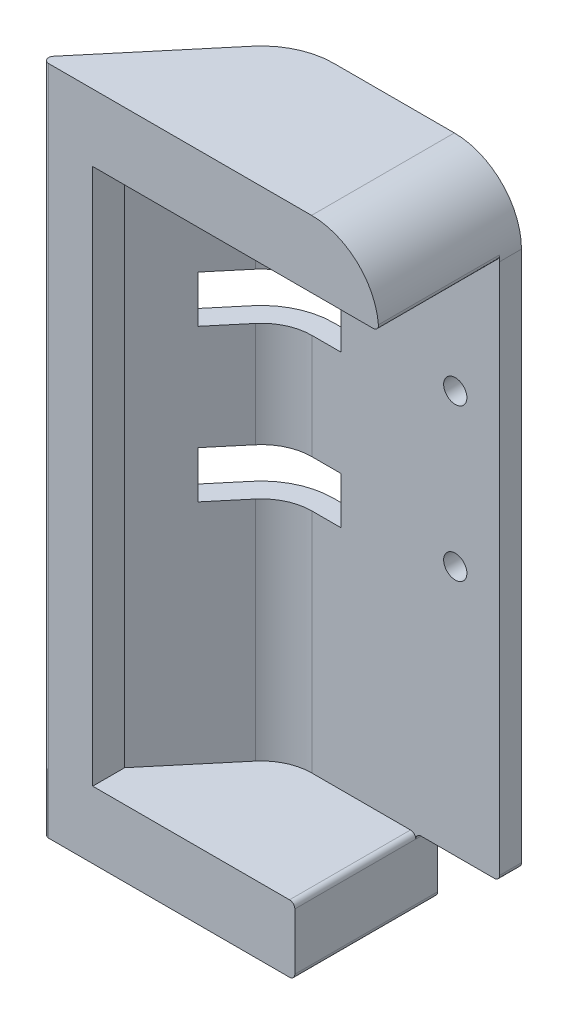
SolidWorks part; units mm, degrees
ref_plane "Front Plane" through (0, 0, 0) normal (0, 0, 1) x (1, 0, 0)
ref_plane "Top Plane" through (0, 0, 0) normal (0, 1, 0) x (1, 0, 0)
ref_plane "Right Plane" through (0, 0, 0) normal (1, 0, 0) x (0, 0, -1)
other "Bounding Box"
ref_plane "Default Plane" through (13.8565, 3.175, 6.7999) normal (0, -1, 0) x (-1, 0, 0)
sketch "Sketch1" plane through (0, 0, 0) normal (0, 1, 0) x (1, 0, 0)
  line L0 (0, 0) -> (-35.56, 0)
  line L1 (-42.8566, -3.4024) -> (-59.217, -22.9)
  line L2 (0, 1.5875) -> (-35.56, 1.5875)
  line L3 (-44.0727, -2.382) -> (-60.4331, -21.8796)
  line L4 (-60.4331, -21.8796) -> (-59.217, -22.9)
  line L5 (0, 1.5875) -> (0, 0)
  arc A0 (-35.56, 0) -> (-42.8566, -3.4024) centre (-35.56, -9.525) ccw
  arc A1 (-35.56, 1.5875) -> (-44.0727, -2.382) centre (-35.56, -9.525) ccw
  dimension "D5" = 9.525
  dimension "D2" = 35.56
  dimension "D3" = 22.9
  dimension "D4" = 130
  dimension "D1" = 1.5875
extrude "Boss-Extrude1" add sketch "Sketch1" along normal blind 127
sketch "Sketch2" plane through (0, 0, -1.5875) normal (0, 0, -1) x (-1, 0, 0)
  line L0 (8.4, 60.1161) -> (8.4, 88.9) construction
  line L1 (8.4, 88.9) -> (40.4616, 88.9) construction
  line L2 (40.4616, 88.9) -> (40.4616, 60.1161) construction
  line L3 (40.4616, 60.1161) -> (8.4, 60.1161) construction
  line L7 (0, 127) -> (35.56, 127) construction
  line L9 (0, 127) -> (0, 0) construction
  line L11 (29.99, 84.455) -> (49.04, 84.455)
  line L12 (29.99, 84.455) -> (29.99, 93.345)
  line L13 (29.99, 93.345) -> (49.04, 93.345)
  line L14 (49.04, 84.455) -> (49.04, 93.345)
  line L15 (29.99, 84.455) -> (49.04, 93.345) construction
  line L16 (29.99, 93.345) -> (49.04, 84.455) construction
  line L17 (29.99, 55.6711) -> (49.04, 55.6711)
  line L18 (29.99, 55.6711) -> (29.99, 64.5611)
  line L19 (29.99, 64.5611) -> (49.04, 64.5611)
  line L20 (49.04, 55.6711) -> (49.04, 64.5611)
  line L21 (29.99, 55.6711) -> (49.04, 64.5611) construction
  line L22 (29.99, 64.5611) -> (49.04, 55.6711) construction
  circle A0 centre (40.4616, 60.1161) radius 2.05 construction
  circle A1 centre (40.4616, 88.9) radius 2.05 construction
  circle A2 centre (8.4, 88.9) radius 2.05
  circle A3 centre (8.4, 60.1161) radius 2.05
  point P12 (39.515, 88.9)
  point P17 (39.515, 60.1161)
  dimension "D3" = 4.1
  dimension "D1" = 28.7839
  dimension "D2" = 32.0616
  dimension "D4" = 38.1
  dimension "D5" = 6.35
  dimension "D6" = 8.89
  dimension "D8" = 19.05
  dimension "D7" = 21.59
extrude "Cut-Extrude1" cut sketch "Sketch2" against normal through all
fillet "Fillet1" radius 12.7 4 edges at (-59.825, 127, 22.3898) (-59.825, 0, 22.3898) (0, 127, -0.7937) (0, 0, -0.7937)
sketch "Sketch4" plane through (-23.4739, 0, -19.6969) normal (0.766, 0, 0.6428) x (0.6428, 0, -0.766)
  line L0 (-39.7738, 93.345) -> (-37.8819, 93.345) construction
  line L1 (-39.7738, 84.455) -> (-39.7738, 93.345) construction
  line L2 (-39.7738, 84.455) -> (-37.8819, 84.455) construction
  line L3 (-37.8819, 93.345) -> (-37.8819, 84.455) construction
  line L4 (-39.7738, 55.6711) -> (-37.8819, 55.6711) construction
  line L5 (-39.7738, 55.6711) -> (-39.7738, 64.5611) construction
  line L6 (-37.8819, 64.5611) -> (-37.8819, 55.6711) construction
  line L7 (-39.7738, 64.5611) -> (-37.8819, 64.5611) construction
  line L8 (-39.7738, 93.345) -> (-37.8819, 93.345)
  line L9 (-39.7738, 84.455) -> (-39.7738, 93.345)
  line L10 (-39.7738, 84.455) -> (-37.8819, 84.455)
  line L11 (-37.8819, 93.345) -> (-37.8819, 84.455)
  line L12 (-39.7738, 55.6711) -> (-37.8819, 55.6711)
  line L13 (-39.7738, 55.6711) -> (-39.7738, 64.5611)
  line L14 (-37.8819, 64.5611) -> (-37.8819, 55.6711)
  line L15 (-39.7738, 64.5611) -> (-37.8819, 64.5611)
extrude "Boss-Extrude2" add sketch "Sketch4" against normal up to surface up to face at (-49.04, 88.9, 9.5367)
sketch "Sketch5" plane through (0, 0, 0) normal (0, -1, 0) x (1, 0, 0)
  line L0 (-44.0727, 2.382) -> (-60.4331, 21.8796)
  line L1 (-59.217, 22.9) -> (0, 22.9)
  line L2 (0, 22.9) -> (0, -1.5875)
  line L3 (0, -1.5875) -> (-35.56, -1.5875)
  line L4 (-44.0727, 2.382) -> (-52.2697, 12.1508) construction
  line L5 (-60.4331, 21.8796) -> (-59.217, 22.9)
  arc A0 (-44.0727, 2.382) -> (-35.56, -1.5875) centre (-35.56, 9.525) ccw construction
  arc A1 (-44.0727, 2.382) -> (-35.56, -1.5875) centre (-35.56, 9.525) ccw
extrude "Boss-Extrude3" add sketch "Sketch5" against normal blind 12.7
sketch "Sketch6" plane through (0, 0, -1.5875) normal (0, 0, -1) x (-1, 0, 0)
  line L1 (0, 0) -> (15.875, 0)
  line L2 (0, 0) -> (0, 12.7)
  line L3 (0, 12.7) -> (15.875, 12.7)
  line L4 (15.875, 0) -> (15.875, 12.7)
  dimension "D1" = 12.7
  dimension "D2" = 15.875
extrude "Cut-Extrude2" cut sketch "Sketch6" against normal through all
sketch "Sketch7" plane through (0, 0, 0) normal (0, -1, 0) x (1, 0, 0)
  line L0 (-59.217, 22.9) -> (-64.605, 22.9)
  line L1 (-64.605, 22.9) -> (-46.0184, 0.7493)
  line L2 (-35.56, -4.1275) -> (0, -4.1275)
  line L3 (0, -4.1275) -> (0, -1.5875)
  line L4 (-52.2697, 12.1508) -> (-51.0536, 13.1712) construction
  line L5 (-15.875, -1.5875) -> (-35.56, -1.5875) construction
  line L6 (-15.875, -1.5875) -> (0, -1.5875) construction
  line L7 (-52.2697, 12.1508) -> (-51.0536, 13.1712)
  line L8 (-15.875, -1.5875) -> (-35.56, -1.5875)
  line L9 (-15.875, -1.5875) -> (0, -1.5875)
  line L10 (-44.0727, 2.382) -> (-52.2697, 12.1508)
  line L11 (-51.0536, 13.1712) -> (-59.217, 22.9)
  arc A1 (-44.0727, 2.382) -> (-35.56, -1.5875) centre (-35.56, 9.525) ccw construction
  arc A2 (-46.0184, 0.7493) -> (-35.56, -4.1275) centre (-35.56, 9.525) ccw
  arc A3 (-46.0184, 0.7493) -> (-35.56, -4.1275) centre (-35.56, 9.525) ccw
  arc A4 (-44.0727, 2.382) -> (-35.56, -1.5875) centre (-35.56, 9.525) ccw
  dimension "D1" = 2.54
extrude "Boss-Extrude4" add sketch "Sketch7" against normal up to surface (127 mm away) up to face at (-35.9487, 127, 3.2724)
sketch "Sketch8" plane through (0, 0, 0) normal (0, 0, 1) x (1, 0, 0)
  line L0 (-12.7, 127) -> (0, 127)
  line L1 (-47.8239, 84.455) -> (-29.99, 84.455)
  line L2 (-47.8239, 84.455) -> (-47.8239, 93.345)
  line L3 (-47.8239, 93.345) -> (-29.99, 93.345)
  line L4 (-29.99, 84.455) -> (-29.99, 93.345)
  line L5 (-29.99, 64.5611) -> (-47.8239, 64.5611)
  line L6 (-29.99, 64.5611) -> (-29.99, 55.6711)
  line L7 (-29.99, 55.6711) -> (-47.8239, 55.6711)
  line L8 (-47.8239, 64.5611) -> (-47.8239, 55.6711)
  line L9 (0, 127) -> (0, 114.3)
  line L11 (-15.875, 12.7) -> (0, 12.7)
  line L12 (-15.875, 12.7) -> (-15.875, 0)
  line L13 (-15.875, 0) -> (0, 0)
  line L14 (0, 12.7) -> (0, 0)
  circle A1 centre (-8.4, 88.9) radius 2.2
  circle A2 centre (-8.4, 60.1161) radius 2.2
  arc A3 (0, 114.3) -> (-12.7, 127) centre (-12.7, 114.3) ccw construction
  arc A4 (0, 114.3) -> (-12.7, 127) centre (-12.7, 114.3) ccw
  dimension "D1" = 4.4
extrude "Cut-Extrude3" cut sketch "Sketch8" against normal through all both and the other way through all
sketch "Sketch9" plane through (-23.4739, 0, -19.6969) normal (0.766, 0, 0.6428) x (0.6428, 0, -0.766)
  line L0 (-30.1541, 55.6711) -> (-37.8819, 55.6711) construction
  line L1 (-37.8819, 93.345) -> (-32.9629, 93.345)
  line L2 (-37.8819, 93.345) -> (-37.8819, 84.455)
  line L3 (-37.8819, 84.455) -> (-32.9629, 84.455)
  line L4 (-32.9629, 93.345) -> (-32.9629, 84.455)
  line L5 (-37.8819, 64.5611) -> (-32.9629, 64.5611)
  line L6 (-37.8819, 64.5611) -> (-37.8819, 55.6711)
  line L7 (-37.8819, 55.6711) -> (-32.9629, 55.6711)
  line L8 (-32.9629, 64.5611) -> (-32.9629, 55.6711)
  line L9 (-32.9629, 55.6711) -> (-35.99, 55.6711) construction
  line L10 (-32.9629, 55.6711) -> (-32.9629, 64.5611) construction
  point P15 (-32.9629, 55.6711)
extrude "Cut-Extrude4" cut sketch "Sketch9" against normal through all
fillet "Fillet2" radius 1 4 edges at (0, 12.7, -2.0637) (-15.875, 12.7, 11.45) (-15.875, 0, 9.3862) (-64.605, 63.5, 22.9)
fillet "Fillet3" radius 1 1 edges at (-15.875, 12.7, -2.0637)
sketch "Sketch10" plane through (0, 12.7, 0) normal (0, 1, 0) x (1, 0, 0)
  line L0 (-59.217, -22.9) -> (-54.137, -22.9)
  line L1 (-16.875, -22.9) -> (-59.217, -22.9) construction
  line L2 (-54.137, -22.9) -> (-54.137, -16.8459)
  line L3 (-59.217, -22.9) -> (-42.8566, -3.4024) construction
  line L4 (-54.137, -16.8459) -> (-59.217, -22.9)
  dimension "D1" = 5.08
extrude "Boss-Extrude5" add sketch "Sketch10" along normal up to surface (114.3 mm away) up to face at (-41.3045, 127, 6.8033)
ref_plane "Plane1" through (0, 114.3, 0) normal (0, 1, 0) x (1, 0, 0)
sketch "Sketch11" plane through (0, 114.3, 0) normal (0, 1, 0) x (1, 0, 0)
  line L0 (-54.137, -22.9) -> (-54.137, -16.8459) construction
  line L1 (-42.8566, -3.4024) -> (-54.137, -16.8459) construction
  line L5 (-54.137, -22.9) -> (-54.137, -16.8459)
  line L6 (-42.8566, -3.4024) -> (-54.137, -16.8459)
  line L11 (-35.56, 0) -> (0, 0)
  line L12 (0, 0) -> (0, -22.9)
  line L13 (0, -22.9) -> (-54.137, -22.9)
  arc A0 (-35.56, 0) -> (-42.8566, -3.4024) centre (-35.56, -9.525) ccw construction
  arc A1 (-35.56, 0) -> (-42.8566, -3.4024) centre (-35.56, -9.525) ccw
extrude "Boss-Extrude6" add sketch "Sketch11" along normal up to surface (12.7 mm away) up to face at (-42.0797, 127, 7.8076)
sketch "Sketch12" plane through (0, 0, 0) normal (0, 0, -1) x (-1, 0, 0)
  line L2 (12.7, 127) -> (0, 127)
  line L3 (0, 127) -> (0, 114.3)
  line L4 (12.7, 127) -> (0, 127)
  line L5 (0, 127) -> (0, 114.3)
  arc A1 (12.7, 127) -> (0, 114.3) centre (12.7, 114.3) ccw
  arc A2 (12.7, 127) -> (0, 114.3) centre (12.7, 114.3) ccw
  dimension "D1" = 0
extrude "Cut-Extrude5" cut sketch "Sketch12" against normal through all
fillet "Fillet4" radius 1 1 edges at (0, 114.3, 11.45)
equation "\"D3@Sketch2\"=4.1mm"
equation "\"D3@Sketch1\"=1.000in-2.5mm"
equation "\"D1@Sketch8\"=4.4mm"
